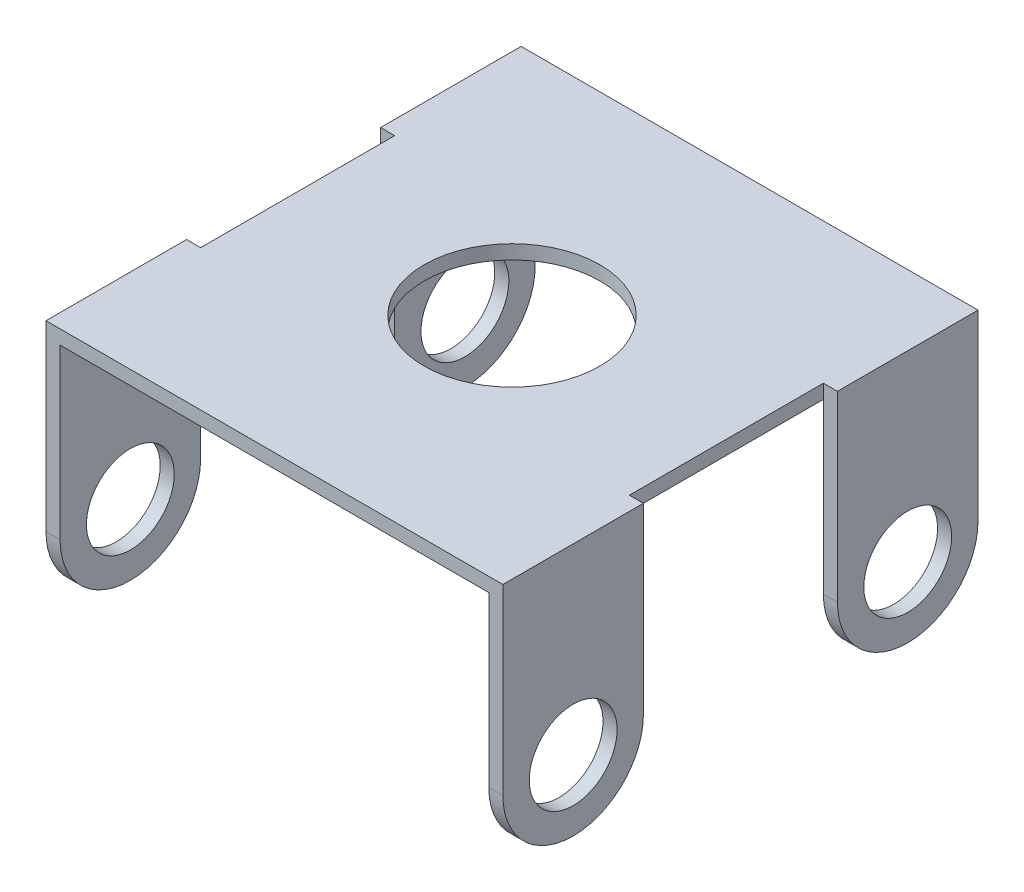
SolidWorks part; units mm, degrees
ref_plane "Front Plane" through (0, 0, 0) normal (0, 0, 1) x (1, 0, 0)
ref_plane "Top Plane" through (0, 0, 0) normal (0, 1, 0) x (1, 0, 0)
ref_plane "Right Plane" through (0, 0, 0) normal (1, 0, 0) x (0, 0, -1)
sketch "Sketch1" plane through (0, 0, 0) normal (0, 1, 0) x (1, 0, 0)
  line L1 (-19.3675, 21.463) -> (19.3675, 21.463)
  line L2 (-19.3675, 21.463) -> (-19.3675, -21.463)
  line L3 (-19.3675, -21.463) -> (19.3675, -21.463)
  line L4 (19.3675, 21.463) -> (19.3675, -21.463)
  line L5 (-19.3675, 21.463) -> (19.3675, -21.463) construction
  line L6 (-19.3675, -21.463) -> (19.3675, 21.463) construction
  point P0 (0, 0)
  dimension "D1" = 38.735
  dimension "D2" = 42.926
extrude "Boss-Extrude1" add sketch "Sketch1" along normal blind 1.27
sketch "Sketch5" plane through (19.3675, 0, 0) normal (1, 0, 0) x (0, 0, -1)
  line L0 (0, 0) -> (0, -23.2132) construction
  line L1 (-21.463, 1.27) -> (-8.763, 1.27)
  line L2 (-21.463, 1.27) -> (-21.463, -15.24)
  line L4 (-8.763, 1.27) -> (-8.763, -15.24)
  line L5 (-21.463, 1.27) -> (-8.763, 1.27)
  arc A0 (-21.463, -15.24) -> (-8.763, -15.24) centre (-15.113, -15.24) ccw
  circle A1 centre (-15.113, -15.24) radius 3.9688
  line M14 (-21.463, 0) -> (21.463, 0)
  line M16 (21.463, 1.27) -> (-21.463, 1.27)
  line M17 (-21.463, 1.27) -> (-21.463, 0)
  dimension "D1" = 15.113
  dimension "D3" = 7.9375
  dimension "D2" = 16.51
  dimension "D4" = 12.7
extrude "Boss-Extrude3" add sketch "Sketch5" along normal blind 1.27 contours L2 A0 L4 A1 M14 | L4 M16 M17 M14
mirror "Mirror1" about plane through (0, 0, 0) normal (0, 0, 1) of "Boss-Extrude3"
mirror "Mirror2" about plane through (0, 0, 0) normal (1, 0, 0) of "Mirror1", "Boss-Extrude3"
sketch "Sketch6" plane through (0, 0, 0) normal (0, 1, 0) x (1, 0, 0)
  circle A0 centre (0, 0) radius 7.9375
  dimension "D1" = 15.875
extrude "Cut-Extrude1" cut sketch "Sketch6" against normal through all both and the other way through all
